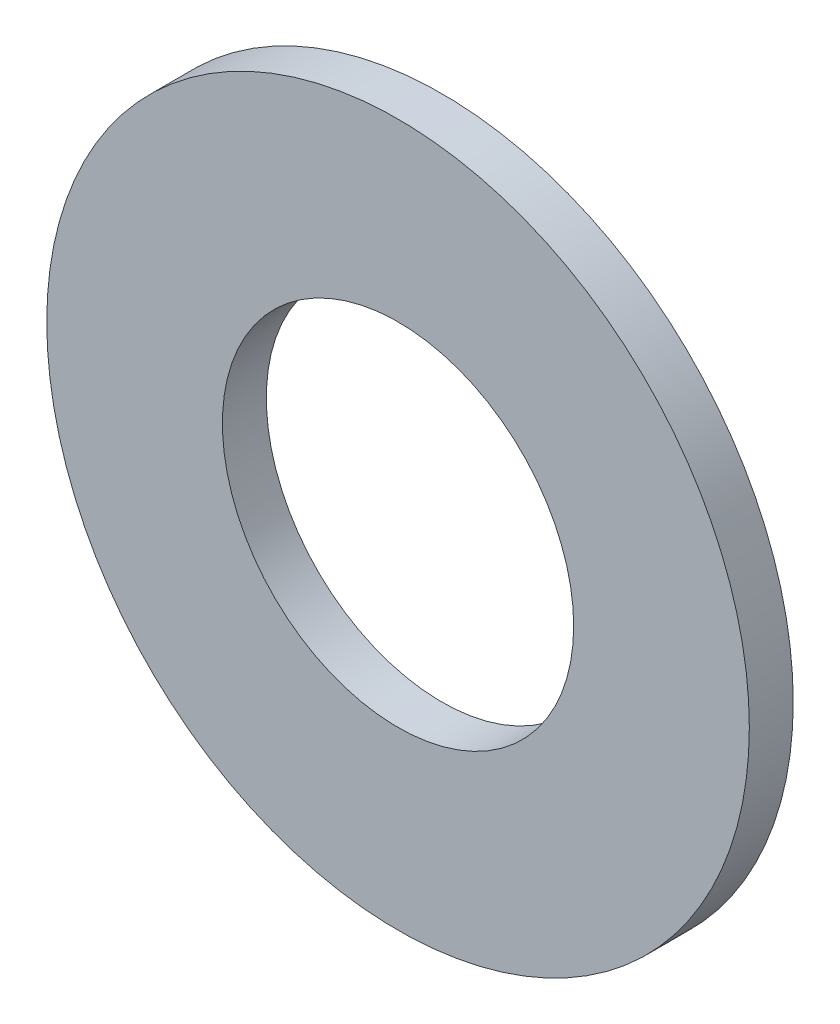
SolidWorks part; units mm, degrees
ref_plane "Płaszczyzna przednia" through (0, 0, 0) normal (0, 0, 1) x (1, 0, 0)
ref_plane "Płaszczyzna górna" through (0, 0, 0) normal (0, 1, 0) x (1, 0, 0)
ref_plane "Płaszczyzna prawa" through (0, 0, 0) normal (1, 0, 0) x (0, 0, -1)
sketch "Szkic1" plane through (0, 0, 0) normal (0, 0, 1) x (1, 0, 0)
  circle A0 centre (0, 0) radius 6
  circle A1 centre (0, 0) radius 12
  dimension "D1" = 12
  dimension "D2" = 24
extrude "Dodanie-wyciągnięcie1" add sketch "Szkic1" along normal blind 1.5
